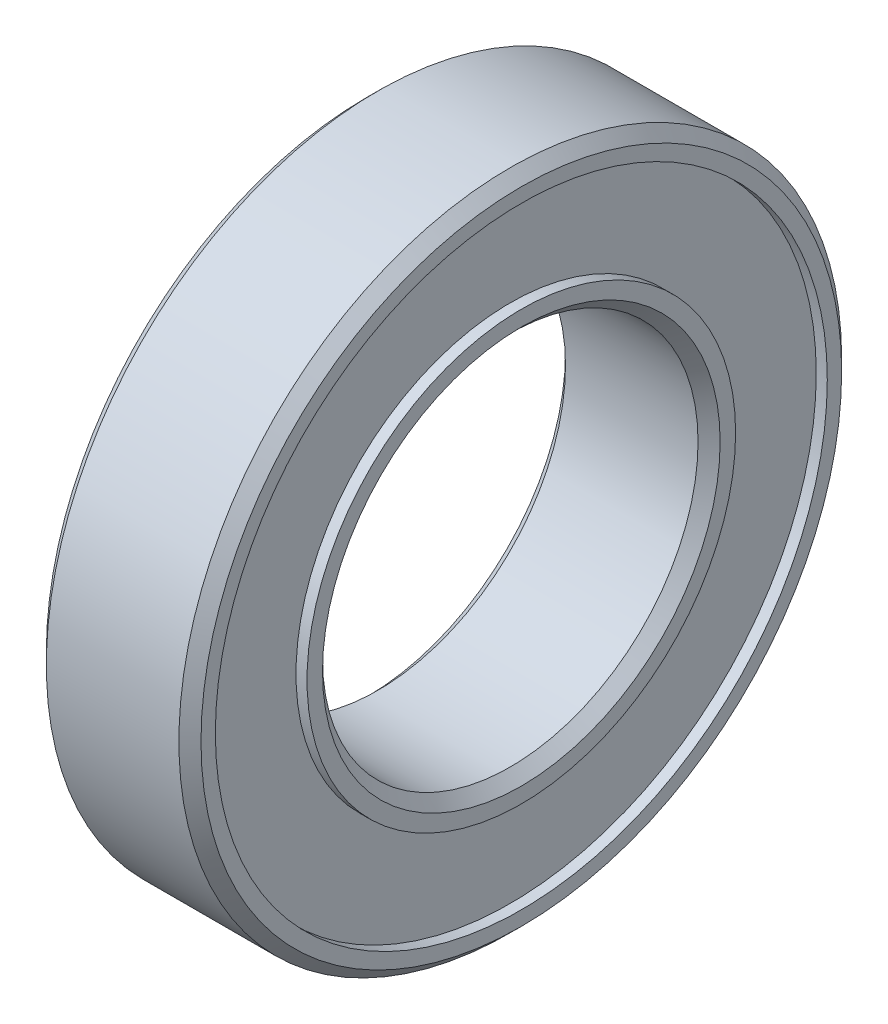
SolidWorks part; units mm, degrees
ref_plane "Front Plane" through (0, 0, 0) normal (0, 0, 1) x (1, 0, 0)
ref_plane "Top Plane" through (0, 0, 0) normal (0, 1, 0) x (1, 0, 0)
ref_plane "Right Plane" through (0, 0, 0) normal (1, 0, 0) x (0, 0, -1)
sketch "Sketch1" plane through (0, 0, 0) normal (1, 0, 0) x (0, 0, -1)
  circle A0 centre (0, 0) radius 8.5
  circle A1 centre (0, 0) radius 15
  dimension "D1" = 17
  dimension "D2" = 30
extrude "Boss-Extrude1" add sketch "Sketch1" along normal blind 7
chamfer "Chamfer1" distance 0.5 angle 45 4 edges at (0, 0, -8.5) (0, 0, -15) (7, 0, -8.5) (7, 0, -15)
sketch "Sketch2" plane through (7, 0, 0) normal (1, 0, 0) x (0, 0, -1)
  circle A0 centre (0, 0) radius 13.85
  circle A1 centre (0, 0) radius 9.7
  dimension "D1" = 19.4
  dimension "D2" = 27.7
extrude "Cut-Extrude1" cut sketch "Sketch2" against normal blind 0.5
sketch "Sketch3" plane through (0, 0, 0) normal (-1, 0, 0) x (0, 0, 1)
  circle A1 centre (0, 0) radius 9.7
  circle A2 centre (0, 0) radius 9.7
  circle A3 centre (0, 0) radius 13.85
  circle A4 centre (0, 0) radius 13.85
  dimension "D1" = 0
  dimension "D2" = 0
extrude "Cut-Extrude2" cut sketch "Sketch3" against normal blind 0.5
